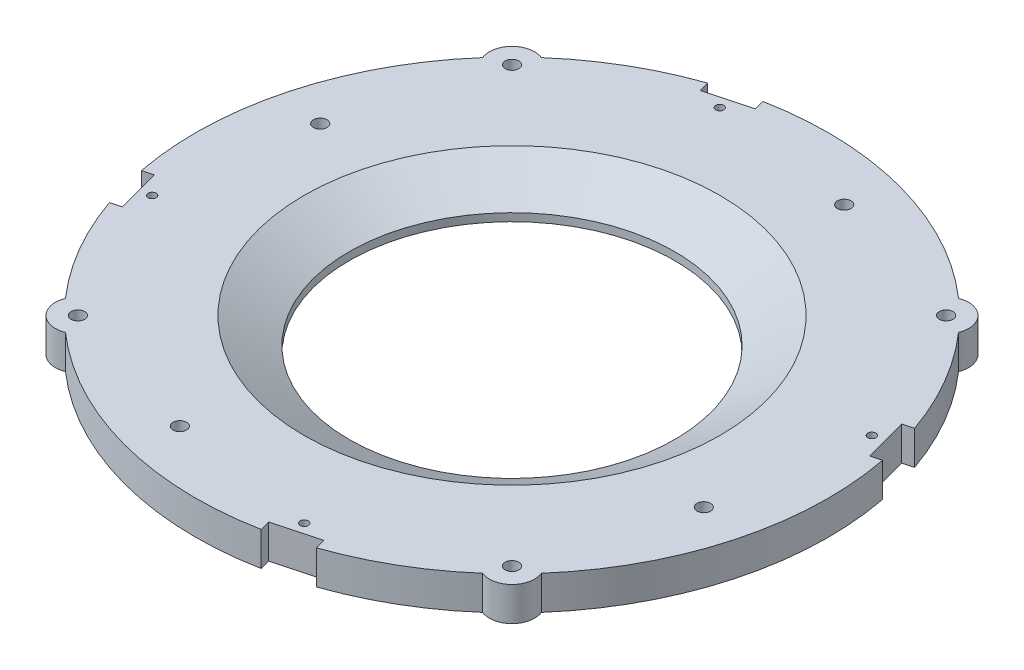
SolidWorks part; units mm, degrees
material "6061-T6 (SS)"
ref_plane "Front Plane" through (0, 0, 0) normal (0, 0, 1) x (1, 0, 0)
ref_plane "Top Plane" through (0, 0, 0) normal (0, 1, 0) x (1, 0, 0)
ref_plane "Right Plane" through (0, 0, 0) normal (1, 0, 0) x (0, 0, -1)
sketch "Sketch1" plane through (0, 0, 0) normal (0, 1, 0) x (1, 0, 0)
  line L0 (0, 88.9) -> (0, -88.9) construction
  line L1 (-88.9, 0) -> (88.9, 0) construction
  line L2 (-60.9759, -60.9759) -> (60.9759, 60.9759) construction
  line L3 (60.9759, -60.9759) -> (-60.9759, 60.9759) construction
  arc A0 (-66.8608, 58.5904) -> (-66.8608, -58.5904) centre (0, 0) ccw
  arc A1 (-58.5904, 66.8608) -> (-66.8608, 58.5904) centre (-60.9759, 60.9759) ccw
  arc A2 (66.8608, 58.5904) -> (58.5904, 66.8608) centre (60.9759, 60.9759) ccw
  arc A3 (58.5904, -66.8608) -> (66.8608, -58.5904) centre (60.9759, -60.9759) ccw
  arc A4 (-66.8608, -58.5904) -> (-58.5904, -66.8608) centre (-60.9759, -60.9759) ccw
  arc A5 (58.5904, 66.8608) -> (-58.5904, 66.8608) centre (0, 0) ccw
  arc A6 (66.8608, -58.5904) -> (66.8608, 58.5904) centre (0, 0) ccw
  arc A7 (-58.5904, -66.8608) -> (58.5904, -66.8608) centre (0, 0) ccw
  circle A8 centre (-60.9759, 60.9759) radius 1.905
  circle A9 centre (60.9759, 60.9759) radius 1.905
  circle A10 centre (60.9759, -60.9759) radius 1.905
  circle A11 centre (-60.9759, -60.9759) radius 1.905
  circle A12 centre (0, 0) radius 83.82 construction
  point P10 (0, 0)
  point P13 (0, 0)
  dimension "D1" = 177.8
  dimension "D3" = 12.7
  dimension "D4" = 3.81
  dimension "D7" = 167.64
  dimension "D2" = 90
  dimension "D5" = 45
  dimension "D6" = 172.466
extrude "Boss-Extrude1" add sketch "Sketch1" along normal blind 9.525
sketch "Sketch2" plane through (0, 9.525, 0) normal (0, 1, 0) x (1, 0, 0)
  circle A0 centre (0, 0) radius 45.72
extrude "Cut-Extrude1" cut sketch "Sketch2" against normal blind 12.7
sketch "Sketch4" plane through (0, 9.525, 0) normal (0, 1, 0) x (1, 0, 0)
  line L0 (0, 0) -> (19.722, 73.6035) construction
  line L2 (0, 0) -> (0, 123.2999) construction
  circle A0 centre (19.722, 73.6035) radius 1.905
  dimension "D1" = 3.81
  dimension "D2" = 76.2
  dimension "D3" = 345
ref_plane "Plane3" through (-62.8618, 0, -62.8618) normal (-0.7071, 0, -0.7071) x (0, -1, 0)
sketch "Sketch10" plane through (-62.8618, 0, -62.8618) normal (-0.7071, 0, -0.7071) x (0, -1, 0)
  line L0 (0, 0) -> (-9.652, 0) construction
  circle A1 centre (-4.826, 0) radius 0.6985
  dimension "D2" = 1.397
  dimension "D1" = 9.652
extrude "Cut-Extrude5" cut sketch "Sketch10" against normal blind 3.175
pattern_circular "CirPattern5" count 4 over 360 about axis through (0, 0, 0) along (0, 1, 0) of "Cut-Extrude5"
chamfer "Chamfer1" distance 12.7 angle 30 1 edges at (0, 9.525, 45.72)
extrude "Cut-Extrude6" cut sketch "Sketch4" against normal through all
pattern_circular "CirPattern6" count 4 over 360 about axis through (0, 0, 0) along (0, 1, 0) of "Cut-Extrude6"
sketch "Sketch13" plane through (0, 9.525, 0) normal (0, 1, 0) x (1, 0, 0)
  line L0 (0, 0) -> (0, 128.7148) construction
  line L1 (0, 0) -> (-35.1918, 131.3375) construction
  circle A0 centre (-21.3655, 79.7372) radius 1.1303
  dimension "D3" = 2.2606
  dimension "D1" = 345
  dimension "D2" = 82.55
extrude "Cut-Extrude7" cut sketch "Sketch13" against normal through all
pattern_circular "CirPattern7" count 4 over 360 about axis through (0, 0, 0) along (0, 1, 0) of "Cut-Extrude7"
ref_plane "Plane4" through (-23.009, 0, -85.8708) normal (-0.2588, 0, -0.9659) x (0, -1, 0)
sketch "Sketch14" plane through (-23.009, 0, -85.8708) normal (-0.2588, 0, -0.9659) x (0, -1, 0)
  line L1 (1.3545, -6.35) -> (-10.5978, -6.35)
  line L2 (1.3545, -6.35) -> (1.3545, 6.35)
  line L3 (1.3545, 6.35) -> (-10.5978, 6.35)
  line L4 (-10.5978, -6.35) -> (-10.5978, 6.35)
  line L5 (1.3545, -6.35) -> (-10.5978, 6.35) construction
  line L6 (1.3545, 6.35) -> (-10.5978, -6.35) construction
  point P0 (-4.6217, 0)
  dimension "D1" = 12.7
extrude "Cut-Extrude8" cut sketch "Sketch14" against normal blind 3.175
pattern_circular "CirPattern8" count 4 over 360 about axis through (0, 0, 0) along (0, 1, 0) of "Cut-Extrude8"
